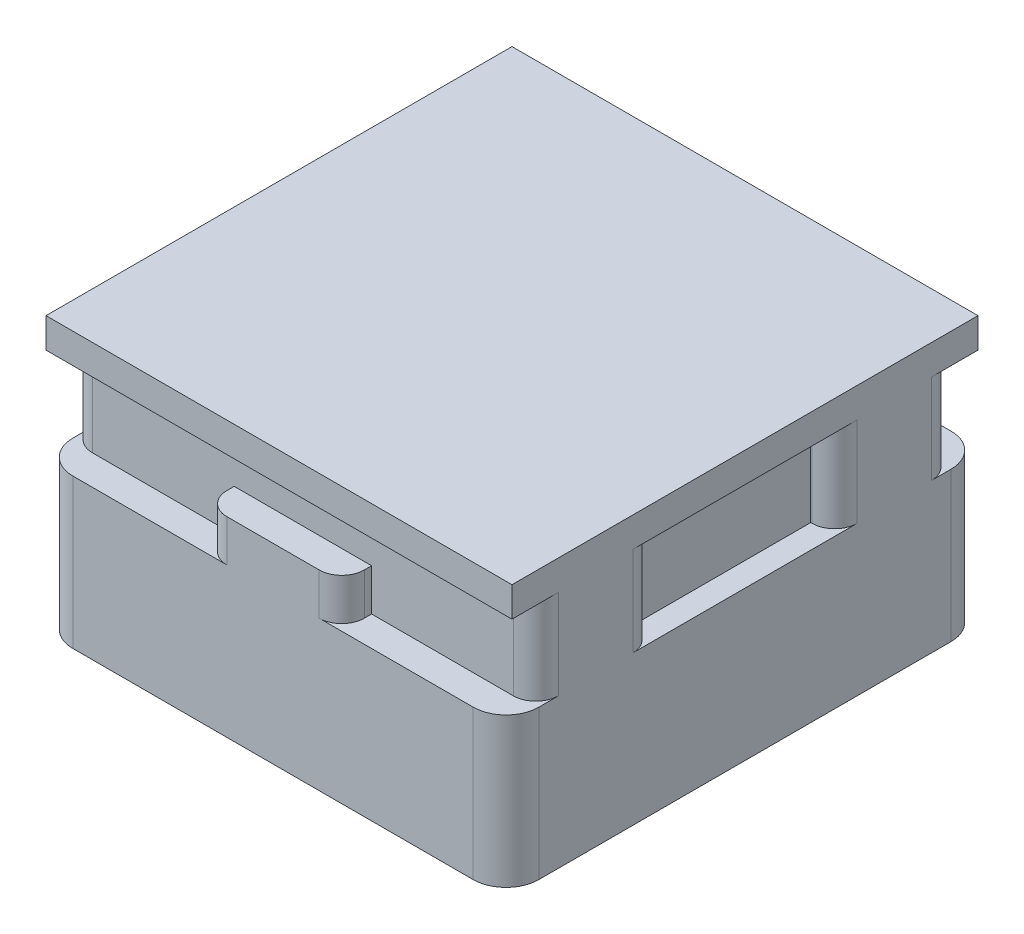
SolidWorks part; units mm, degrees
ref_plane "Front Plane" through (0, 0, 0) normal (0, 0, 1) x (1, 0, 0)
ref_plane "Top Plane" through (0, 0, 0) normal (0, 1, 0) x (1, 0, 0)
ref_plane "Right Plane" through (0, 0, 0) normal (1, 0, 0) x (0, 0, -1)
sketch "Sketch5" plane through (0, 0, 0) normal (0, 0, -1) x (0, -1, 0)
  line L0 (0, 0) -> (9, 0) construction
  point P3 (3, 0)
  dimension "D1" = 6
  dimension "D2" = 3
ref_plane "pl Lock lip" through (0, -1.6, 0) normal (0, 1, 0) x (-1, 0, 0)
ref_plane "pl Switch Top plate" through (0, -3, 0) normal (0, 1, 0) x (-1, 0, 0)
ref_plane "pl Switch Room" through (0, -9, 0) normal (0, 1, 0) x (1, 0, 0)
sketch "Sketch2" plane through (0, 0, 0) normal (0, 1, 0) x (1, 0, 0)
  line L0 (0, 7.8) -> (0, -7.8) construction
  line L1 (-7.8, -7.8) -> (7.8, -7.8)
  line L2 (-7.8, -7.8) -> (-7.8, 7.8)
  line L3 (-7.8, 7.8) -> (7.8, 7.8)
  line L4 (7.8, -7.8) -> (7.8, 7.8)
  point P6 (0, 0)
  dimension "D1" = 15.6
extrude "Boss-Extrude2" add sketch "Sketch2" along normal blind 1 separate body
sketch "Cutout" plane through (0, 0, 0) normal (0, 1, 0) x (1, 0, 0)
  line L0 (-7, 0) -> (7, 0) construction
  line L2 (-7, -7) -> (-7, 7) construction
  line L4 (7, -7) -> (7, 7) construction
  line L5 (-7.8, 3) -> (-7, 3)
  line L6 (0, 3) -> (0, 0) construction
  line L7 (-7.8, -3) -> (7.8, -3) construction
  line L9 (-7.8, -7) -> (-7.8, 7) construction
  line L11 (7.8, 7) -> (7.8, -7) construction
  line L13 (-7.8, 3) -> (7.8, 3) construction
  line L15 (0, 0) -> (0, -3) construction
  line L20 (7.8, 3) -> (7, 3)
  line L21 (7, 3) -> (7, -3)
  line L22 (7, -3) -> (7.8, -3)
  line L27 (-7.8, -3) -> (-7, -3)
  line L28 (-7, -3) -> (-7, 3)
  line L29 (7.8, -7) -> (-7.8, -7)
  line L30 (-7.8, 7) -> (7.8, 7)
  line L31 (-7.8, 7) -> (-7.8, 3)
  line L32 (7.8, 7) -> (7.8, 3)
  line L33 (7.8, -3) -> (7.8, -7)
  line L34 (-7.8, -7) -> (-7.8, -3)
  dimension "D1" = 14
  dimension "D2" = 15.6
  dimension "D3" = 6
  dimension "D4" = 14
extrude "Boss-Extrude1" add sketch "Cutout" against normal up to surface (3 mm away) up to plane "pl Switch Top plate"
sketch "Sketch3" plane through (0, -1.6, 0) normal (0, 1, 0) x (-1, 0, 0)
  line L0 (-7.8, 7) -> (7.8, 7) construction
  line L1 (-7.8, 7) -> (7.8, 7) construction
  line L2 (0, 0) -> (0, 11.0036) construction
  line L3 (2.3, 7) -> (-2.3, 7)
  line L4 (2.3, 7) -> (2.3, 8)
  line L5 (2.3, 8) -> (-2.3, 8)
  line L6 (-2.3, 7) -> (-2.3, 8)
  dimension "D2" = 1
  dimension "D1" = 4.6
extrude "Boss-Extrude3" add sketch "Sketch3" against normal up to surface (1.4 mm away) up to face at (0, -3, 0)
mirror "Mirror1" about plane through (0, 0, 0) normal (0, 0, 1) of "Boss-Extrude3"
fillet "Fillet1" radius 0.755 12 edges at (2.3, -2.3, -8) (-2.3, -2.3, -8) (2.3, -2.3, 8) (-2.3, -2.3, 8)
sketch "Sketch4" plane through (0, -3, 0) normal (0, -1, 0) x (1, 0, 0)
  line L0 (7.8, -6.245) -> (7.8, -3.755) construction
  line L1 (-6.7, -8) -> (6.7, -8)
  line L2 (-7.8, -6.9) -> (-7.8, 6.9)
  line L3 (-6.7, 8) -> (6.7, 8)
  line L4 (7.8, -6.9) -> (7.8, 6.9)
  line L5 (1.545, -8) -> (-1.545, -8) construction
  line L6 (1.545, 8) -> (-1.545, 8) construction
  line L7 (-7.8, 6.245) -> (-7.8, 3.755) construction
  arc A0 (6.7, 8) -> (7.8, 6.9) centre (6.7, 6.9) cw
  arc A1 (6.7, -8) -> (7.8, -6.9) centre (6.7, -6.9) ccw
  arc A2 (-6.7, -8) -> (-7.8, -6.9) centre (-6.7, -6.9) cw
  arc A3 (-6.7, 8) -> (-7.8, 6.9) centre (-6.7, 6.9) ccw
  dimension "D1" = 1.1
extrude "Boss-Extrude4" add sketch "Sketch4" along normal offset from surface (5 mm away) 1 up to plane "pl Switch Room"
equation "\"D4@Cutout\"=\"D1@Cutout\""
equation "\"Plate2_thickness\"= 6"
equation "\"Top_Plate_thickness\"= 3"
equation "\"D1@Sketch5\"=\"Plate2_thickness\""
equation "\"D2@Sketch5\"=\"Top_Plate_thickness\""
